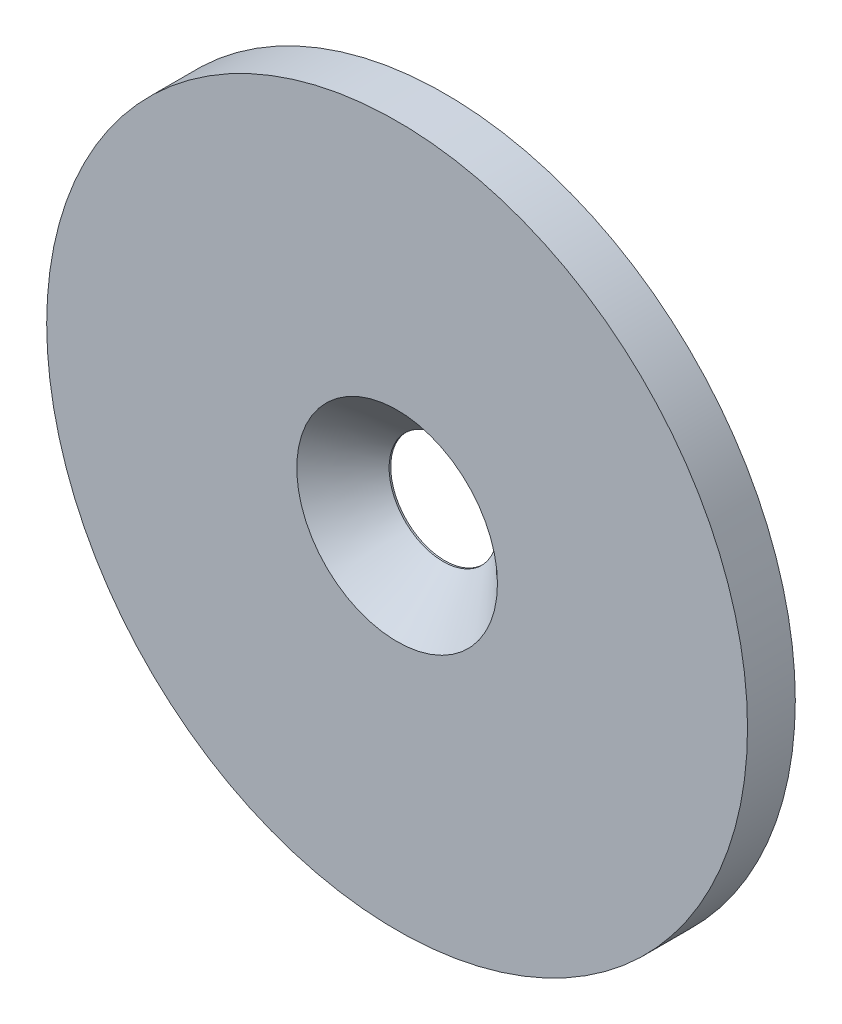
SolidWorks part; units mm, degrees
ref_plane "Front Plane" through (0, 0, 0) normal (0, 0, 1) x (1, 0, 0)
ref_plane "Top Plane" through (0, 0, 0) normal (0, 1, 0) x (1, 0, 0)
ref_plane "Right Plane" through (0, 0, 0) normal (1, 0, 0) x (0, 0, -1)
sketch "Sketch1" plane through (0, 0, 0) normal (0, 0, 1) x (1, 0, 0)
  circle A0 centre (0, 0) radius 1.5
  circle A1 centre (0, 0) radius 11
  dimension "D1" = 3
  dimension "D2" = 22
extrude "Boss-Extrude1" add sketch "Sketch1" along normal blind 1.5
hole_wizard "CSK for M3 Flat Head Machine Screw1" positions "Sketch3" profile "Sketch2" countersink size "M3" standard "Ansi Metric" end condition through all
sketch "Sketch3" plane through (0, 0, 1.5) normal (0, 0, 1) x (1, 0, 0)
  point P0 (0, 0)
sketch "Sketch2" plane through (0, 0, 1.5) normal (1, 0, 0) x (0, -1, 0)
  line L0 (0, 0) -> (0, 1.5)
  line L1 (0, 1.5) -> (1.7, 1.5)
  line L2 (1.7, 1.5) -> (1.7, 1.45)
  line L3 (1.7, 1.45) -> (3.15, 0)
  line L5 (3.15, 0) -> (0, 0)
  line L6 (-1.7, 1.45) -> (-3.15, 0) construction
  line L11 (0, -6.35) -> (0, 107.95) construction
  dimension "Thru Hole Dia." = 3.4
  dimension "Thru Hole Depth" = 1.5
  dimension "Near C'Sink Dia." = 6.3
  dimension "Near C'Sink Angle" = 90
